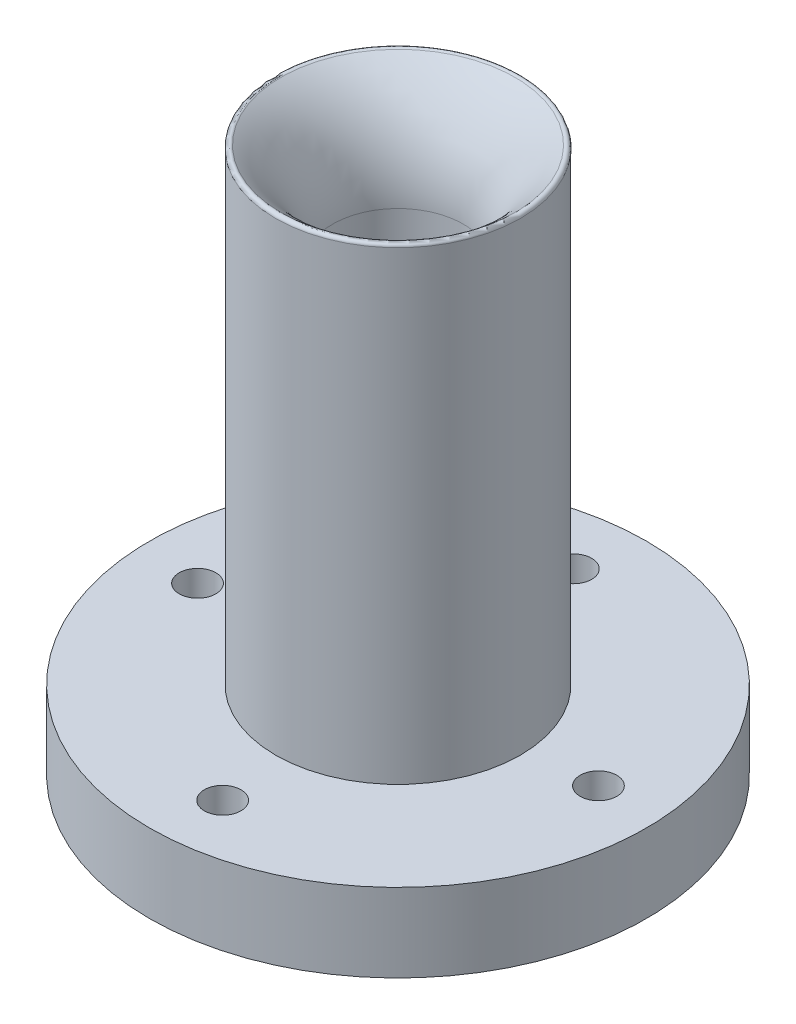
SolidWorks part; units mm, degrees
ref_plane "Front Plane" through (0, 0, 0) normal (0, 0, 1) x (1, 0, 0)
ref_plane "Top Plane" through (0, 0, 0) normal (0, 1, 0) x (1, 0, 0)
ref_plane "Right Plane" through (0, 0, 0) normal (1, 0, 0) x (0, 0, -1)
sketch "Sketch1" plane through (0, 0, 0) normal (0, 0, 1) x (1, 0, 0)
  line L0 (12.5, -14.9726) -> (17.4332, -14.9726)
  line L1 (0, 0) -> (12.5, 0)
  line L2 (0, 0) -> (0, -14.9726)
  line L3 (0, -14.9726) -> (12.5, -14.9726)
  line L4 (23.3921, 88.8749) -> (23.3921, 0.0274)
  line L6 (12.5, 0) -> (12.5, 70)
  line L9 (23.3921, 0.0274) -> (47.5, 0.0274)
  line L11 (17.4332, -14.9726) -> (47.5, -14.9726)
  line L12 (47.5, 0.0274) -> (47.5, -14.9726)
  arc A0 (12.5, 70) -> (22.3816, 89.3642) centre (36.4141, 70) cw
  arc A1 (23.3921, 88.8749) -> (22.3816, 89.3642) centre (22.7684, 88.8749) ccw
  dimension "D2" = 15
  dimension "D3" = 12.5
  dimension "D4" = 47.5
revolve "Revolve1" add sketch "Sketch1" angle 360 about L2
sketch "Sketch2" plane through (0, 0.0274, 0) normal (0, 1, 0) x (1, 0, 0)
  circle A1 centre (-2.3974, 35.9201) radius 3.5
  circle A3 centre (-35.9201, -2.3974) radius 3.5
  circle A4 centre (2.3974, -35.9201) radius 3.5
  circle A5 centre (35.9201, 2.3974) radius 3.5
extrude "Cut-Extrude1" cut sketch "Sketch2" against normal blind 20
